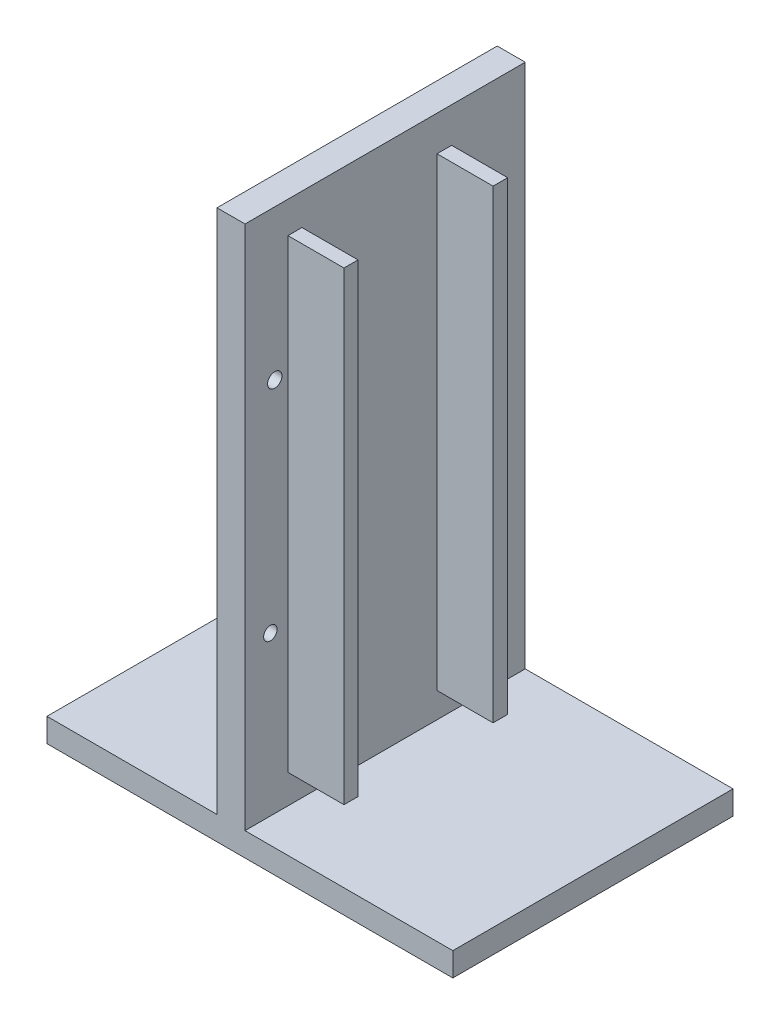
SolidWorks part; units mm, degrees
ref_plane "Front Plane" through (0, 0, 0) normal (0, 0, 1) x (1, 0, 0)
ref_plane "Top Plane" through (0, 0, 0) normal (0, 1, 0) x (1, 0, 0)
ref_plane "Right Plane" through (0, 0, 0) normal (1, 0, 0) x (0, 0, -1)
sketch "Sketch5" plane through (0, 0, 0) normal (0, 0, 1) x (1, 0, 0)
  line L1 (0, 0) -> (73.5771, 0)
  line L2 (0, 0) -> (0, 99.5474)
  line L3 (0, 99.5474) -> (73.5771, 99.5474)
  line L4 (73.5771, 0) -> (73.5771, 99.5474)
extrude "Boss-Extrude2" add sketch "Sketch5" along normal blind 50.8
sketch "Sketch6" plane through (0, 0, 50.8) normal (0, 0, 1) x (1, 0, 0)
  line L1 (0, 99.5474) -> (30.8264, 99.5474)
  line L2 (0, 99.5474) -> (0, 4.2974)
  line L3 (0, 4.2974) -> (30.8264, 4.2974)
  line L4 (30.8264, 99.5474) -> (30.8264, 4.2974)
  dimension "D1" = 95.25
extrude "Cut-Extrude3" cut sketch "Sketch6" against normal blind 50.8
sketch "Sketch7" plane through (0, 0, 50.8) normal (0, 0, 1) x (1, 0, 0)
  line L0 (30.8264, 4.2974) -> (30.8264, 99.5474) construction
  line L1 (73.5771, 99.5474) -> (35.9064, 99.5474)
  line L2 (73.5771, 99.5474) -> (73.5771, 4.2974)
  line L3 (73.5771, 4.2974) -> (35.9064, 4.2974)
  line L4 (35.9064, 99.5474) -> (35.9064, 4.2974)
  dimension "D1" = 95.25
  dimension "D2" = 5.08
extrude "Cut-Extrude4" cut sketch "Sketch7" against normal blind 50.8
sketch "Sketch8" plane through (35.9064, 0, 0) normal (1, 0, 0) x (0, 0, -1)
  line L1 (-43.0215, 93.8274) -> (-40.4815, 93.8274)
  line L2 (-43.0215, 93.8274) -> (-43.0215, 9.5622)
  line L3 (-43.0215, 9.5622) -> (-40.4815, 9.5622)
  line L4 (-40.4815, 93.8274) -> (-40.4815, 9.5622)
  dimension "D1" = 2.54
extrude "Boss-Extrude3" add sketch "Sketch8" along normal blind 10.16
sketch "Sketch9" plane through (35.9064, 0, 0) normal (1, 0, 0) x (0, 0, -1)
  line L1 (-15.993, 93.165) -> (-13.3432, 93.165)
  line L2 (-15.993, 93.165) -> (-15.993, 8.8998)
  line L3 (-15.993, 8.8998) -> (-13.3432, 8.8998)
  line L4 (-13.3432, 93.165) -> (-13.3432, 8.8998)
  dimension "D1" = 2.6498
extrude "Boss-Extrude4" add sketch "Sketch9" along normal blind 10.16
sketch "Sketch10" plane through (35.9064, 0, 0) normal (1, 0, 0) x (0, 0, -1)
  circle A0 centre (-45.4064, 72.3637) radius 1.3049
extrude "Cut-Extrude5" cut sketch "Sketch10" against normal blind 10.16
sketch "Sketch11" plane through (35.9064, 0, 0) normal (1, 0, 0) x (0, 0, -1)
  circle A0 centre (-10.9583, 73.1586) radius 1.3249
extrude "Cut-Extrude6" cut sketch "Sketch11" against normal blind 10.16
sketch "Sketch12" plane through (35.9064, 0, 0) normal (1, 0, 0) x (0, 0, -1)
  circle A0 centre (-46.2013, 33.0134) radius 1.2215
extrude "Cut-Extrude7" cut sketch "Sketch12" against normal blind 10.16
sketch "Sketch13" plane through (35.9064, 0, 0) normal (1, 0, 0) x (0, 0, -1)
  circle A0 centre (-11.3558, 30.8935) radius 1.3641
extrude "Cut-Extrude8" cut sketch "Sketch13" against normal blind 10.16
